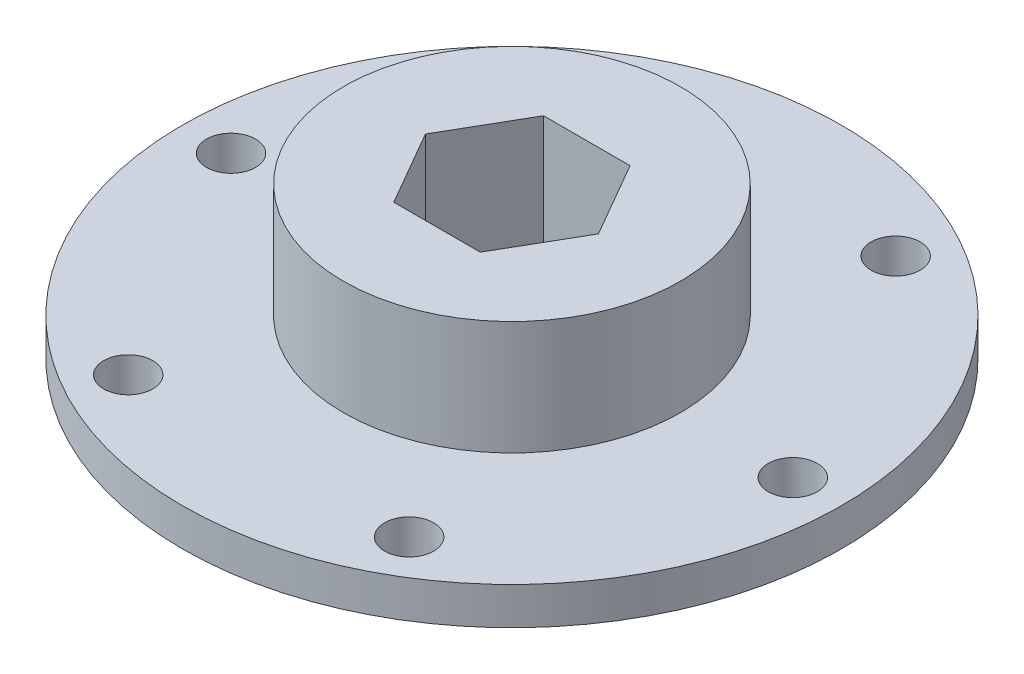
SolidWorks part; units mm, degrees
material "6061-T6 (SS)"
ref_plane "Front Plane" through (0, 0, 0) normal (0, 0, 1) x (1, 0, 0)
ref_plane "Top Plane" through (0, 0, 0) normal (0, 1, 0) x (1, 0, 0)
ref_plane "Right Plane" through (0, 0, 0) normal (1, 0, 0) x (0, 0, -1)
sketch "Sketch1" plane through (0, 0, 0) normal (0, 1, 0) x (1, 0, 0)
  circle A0 centre (0, 0) radius 27.94
  dimension "D1" = 55.88
extrude "Boss-Extrude1" add sketch "Sketch1" along normal blind 3.175
sketch "Sketch2" plane through (0, 3.175, 0) normal (0, 1, 0) x (1, 0, 0)
  circle A0 centre (0, 0) radius 14.2875
  dimension "D1" = 28.575
extrude "Boss-Extrude2" add sketch "Sketch2" along normal blind 9.652
sketch "Sketch3" plane through (0, 0, 0) normal (0, -1, 0) x (1, 0, 0)
  line L0 (-7.3323, 0) -> (7.3323, 0) construction
  line L1 (3.6662, -6.35) -> (7.3323, 0)
  line L2 (7.3323, 0) -> (3.6662, 6.35)
  line L3 (3.6662, 6.35) -> (-3.6662, 6.35)
  line L4 (-3.6662, 6.35) -> (-7.3323, 0)
  line L5 (-7.3323, 0) -> (-3.6662, -6.35)
  line L6 (-3.6662, -6.35) -> (3.6662, -6.35)
  circle A0 centre (0, 0) radius 6.35 construction
  dimension "D1" = 12.7
extrude "Cut-Extrude1" cut sketch "Sketch3" against normal through all
sketch "Sketch4" plane through (0, 0, 0) normal (0, -1, 0) x (1, 0, 0)
  circle A0 centre (-11.9062, 20.6222) radius 2.0828
  circle A1 centre (11.9063, 20.6222) radius 2.0828
  circle A2 centre (23.8125, 0) radius 2.0828
  circle A3 centre (11.9062, -20.6222) radius 2.0828
  circle A4 centre (-11.9063, -20.6222) radius 2.0828
  circle A5 centre (-23.8125, 0) radius 2.0828
  circle A6 centre (0, 0) radius 23.8125 construction
  point P14 (0, 0)
  dimension "D1" = 6
  dimension "D2" = 47.625
  dimension "D3" = 4.1656
extrude "Cut-Extrude2" cut sketch "Sketch4" against normal through all
